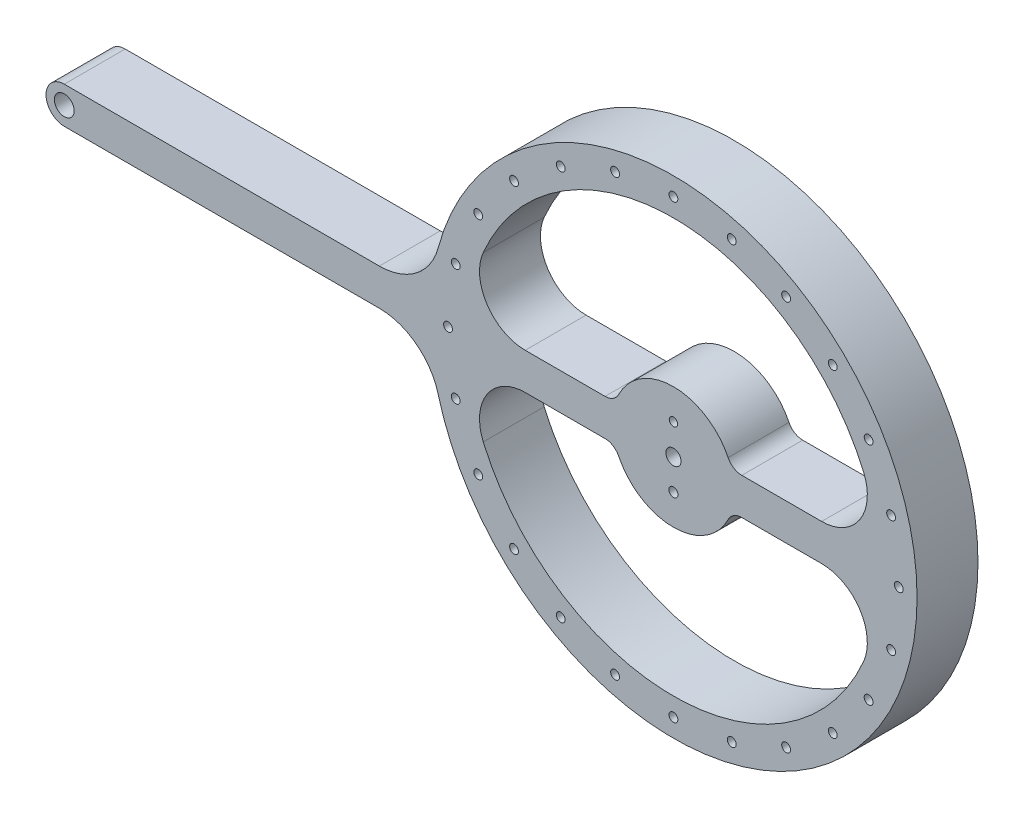
SolidWorks part; units mm, degrees
ref_plane "Front Plane" through (0, 0, 0) normal (0, 0, 1) x (1, 0, 0)
ref_plane "Top Plane" through (0, 0, 0) normal (0, 1, 0) x (1, 0, 0)
ref_plane "Right Plane" through (0, 0, 0) normal (1, 0, 0) x (0, 0, -1)
sketch "Sketch1" plane through (0, 0, 0) normal (0, 0, 1) x (1, 0, 0)
  line L0 (-155.3529, 10.2117) -> (-51.9137, 10.2117)
  line L1 (-4.015, 10.2117) -> (22.1972, 10.2117)
  line L2 (67.0971, 10.2117) -> (93.3092, 10.2117)
  line L3 (93.3092, 22.2117) -> (67.0971, 22.2117)
  line L4 (22.1972, 22.2117) -> (-4.015, 22.2117)
  line L5 (-51.9137, 22.2117) -> (-155.3529, 22.2117)
  arc A0 (-32.6016, -4.5883) -> (-51.9137, 10.2117) centre (-51.9137, -9.7883) ccw
  circle A1 centre (-19.4388, -20.7883) radius 1.45
  circle A2 centre (-26.8314, -2.9409) radius 1.45
  arc A3 (-51.9137, 22.2117) -> (-32.6016, 37.0117) centre (-51.9137, 42.2117) ccw
  arc A4 (-155.3529, 22.2117) -> (-155.3529, 10.2117) centre (-155.3529, 16.2117) ccw
  circle A5 centre (-155.3529, 16.2117) radius 3.25
  circle A6 centre (-26.8314, 35.3643) radius 1.45
  circle A7 centre (-19.4388, 53.2117) radius 1.45
  circle A8 centre (-29.3529, 16.2117) radius 1.45
  arc A9 (107.0815, -10.7317) -> (93.3092, 10.2117) centre (93.3092, -4.7883) ccw
  arc A10 (-4.015, 10.2117) -> (-17.7873, -10.7317) centre (-4.015, -4.7883) ccw
  arc A11 (67.0971, 10.2117) -> (62.6071, 7.4117) centre (67.0971, 5.2117) ccw
  arc A12 (26.6872, 7.4117) -> (22.1972, 10.2117) centre (22.1972, 5.2117) ccw
  circle A13 centre (44.6471, 6.2117) radius 1.5
  circle A14 centre (116.1256, -2.9409) radius 1.45
  circle A15 centre (108.733, -20.7883) radius 1.45
  circle A16 centre (96.973, -36.1142) radius 1.45
  circle A17 centre (81.6471, -47.8742) radius 1.45
  circle A18 centre (63.7997, -55.2668) radius 1.45
  circle A19 centre (44.6471, -57.7883) radius 1.45
  circle A20 centre (25.4945, -55.2668) radius 1.45
  circle A21 centre (7.6471, -47.8742) radius 1.45
  circle A22 centre (-7.6788, -36.1142) radius 1.45
  arc A23 (124.5879, 13.1348) -> (-32.6016, 37.0117) centre (44.6471, 16.2117) ccw
  arc A24 (-32.6016, -4.5883) -> (124.5879, 13.1348) centre (44.6471, 16.2117) ccw
  arc A25 (-17.7873, -10.7317) -> (107.0815, -10.7317) centre (44.6471, 16.2117) ccw
  arc A26 (107.0815, 43.1551) -> (-17.7873, 43.1551) centre (44.6471, 16.2117) ccw
  arc A27 (26.6872, 7.4117) -> (62.6071, 7.4117) centre (44.6471, 16.2117) ccw
  arc A28 (62.6071, 25.0117) -> (26.6872, 25.0117) centre (44.6471, 16.2117) ccw
  arc A29 (93.3092, 22.2117) -> (107.0815, 43.1551) centre (93.3092, 37.2117) ccw
  arc A30 (-17.7873, 43.1551) -> (-4.015, 22.2117) centre (-4.015, 37.2117) ccw
  arc A31 (62.6071, 25.0117) -> (67.0971, 22.2117) centre (67.0971, 27.2117) ccw
  arc A32 (22.1972, 22.2117) -> (26.6872, 25.0117) centre (22.1972, 27.2117) ccw
  circle A33 centre (44.6471, 16.2117) radius 2.5
  circle A34 centre (-7.6788, 68.5376) radius 1.45
  circle A35 centre (7.6471, 80.2976) radius 1.45
  circle A36 centre (25.4945, 87.6902) radius 1.45
  circle A37 centre (44.6471, 90.2117) radius 1.45
  circle A38 centre (63.7997, 87.6902) radius 1.45
  circle A39 centre (81.6471, 80.2976) radius 1.45
  circle A40 centre (96.973, 68.5376) radius 1.45
  circle A41 centre (108.733, 53.2117) radius 1.45
  circle A42 centre (116.1256, 35.3643) radius 1.45
  circle A43 centre (44.6471, 26.2117) radius 1.375
  circle A44 centre (118.6471, 16.2117) radius 1.45
  dimension "D1" = 5
extrude "Boss-Extrude2" add sketch "Sketch1" along normal blind 20
